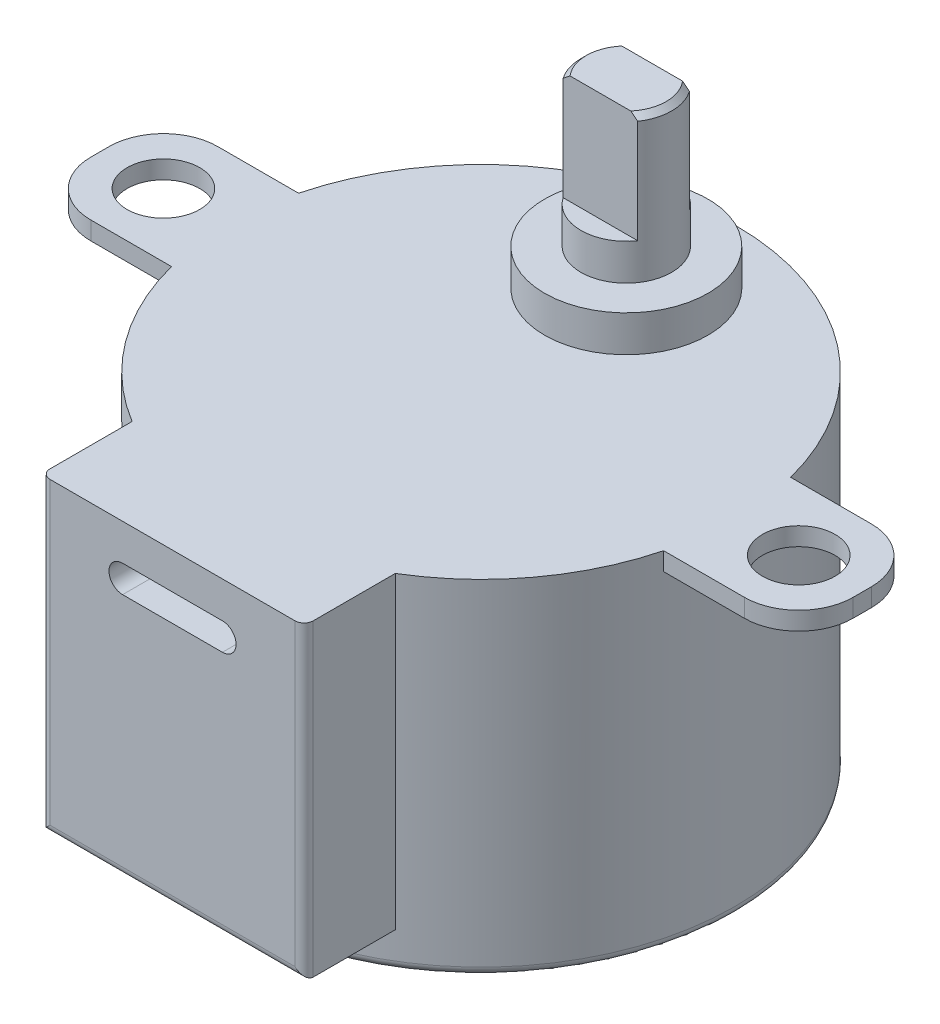
SolidWorks part; units mm, degrees
ref_plane "Спереди" through (0, 0, 0) normal (0, 0, 1) x (1, 0, 0)
ref_plane "Сверху" through (0, 0, 0) normal (0, 1, 0) x (1, 0, 0)
ref_plane "Справа" through (0, 0, 0) normal (1, 0, 0) x (0, 0, -1)
sketch "Эскиз1" plane through (0, 0, 0) normal (0, 1, 0) x (1, 0, 0)
  line L0 (-14, 0) -> (14, 0) construction
  line L1 (0, 14) -> (0, -14) construction
  circle A0 centre (0, 0) radius 14
extrude "Бобышка-Вытянуть1" add sketch "Эскиз1" along normal blind 19 contours A0
sketch "Эскиз2" plane through (0, 19, 0) normal (0, 1, 0) x (1, 0, 0)
  line L0 (-18, -3.5) -> (-13.5554, -3.5)
  line L1 (-18, 3.5) -> (-13.5554, 3.5)
  line L2 (-21, 0.5) -> (-21, -0.5)
  line L4 (0, -14) -> (0, 14) construction
  line L5 (-14, 0) -> (14, 0) construction
  line L7 (21, 0.5) -> (21, -0.5)
  line L8 (18, 3.5) -> (13.5554, 3.5)
  line L9 (18, -3.5) -> (13.5554, -3.5)
  arc A0 (-21, 0.5) -> (-18, 3.5) centre (-18, 0.5) cw
  arc A1 (-21, -0.5) -> (-18, -3.5) centre (-18, -0.5) ccw
  circle A2 centre (-17.5, 0) radius 2
  circle A3 centre (0, 0) radius 14 construction
  circle A4 centre (17.5, 0) radius 2
  arc A5 (21, -0.5) -> (18, -3.5) centre (18, -0.5) cw
  arc A6 (21, 0.5) -> (18, 3.5) centre (18, 0.5) ccw
  point P25 (21, 0)
  circle M6 centre (0, 0) radius 14
  dimension "D4" = 3.5
  dimension "D6" = 3
extrude "Бобышка-Вытянуть2" add sketch "Эскиз2" against normal blind 1 contours L7 A6 L8 L9 A5 A4 M6 | L2 A1 L0 L1 A0 A2 M6
sketch "Эскиз5" plane through (0, 19, 0) normal (0, 1, 0) x (1, 0, 0)
  line L1 (-7.25, -17) -> (7.25, -17)
  line L2 (7.25, -17) -> (7.25, -11.9765)
  line L3 (-7.25, -17) -> (-7.25, -11.9765)
  line L9 (-13.5554, 3.5) -> (-18, 3.5)
  line L10 (-21, 0.5) -> (-21, -0.5)
  line L11 (-18, -3.5) -> (-13.5554, -3.5)
  line L12 (13.5554, -3.5) -> (18, -3.5)
  line L13 (21, -0.5) -> (21, 0.5)
  line L14 (18, 3.5) -> (13.5554, 3.5)
  arc A0 (-13.5554, -3.5) -> (13.5554, -3.5) centre (0, 0) ccw construction
  arc A7 (13.5554, 3.5) -> (-13.5554, 3.5) centre (0, 0) ccw
  arc A8 (-18, 3.5) -> (-21, 0.5) centre (-18, 0.5) ccw
  arc A9 (-21, -0.5) -> (-18, -3.5) centre (-18, -0.5) ccw
  arc A10 (-13.5554, -3.5) -> (13.5554, -3.5) centre (0, 0) ccw
  arc A11 (18, -3.5) -> (21, -0.5) centre (18, -0.5) ccw
  arc A12 (21, 0.5) -> (18, 3.5) centre (18, 0.5) ccw
  arc A16 (-7.25, -11.9765) -> (7.25, -11.9765) centre (0, 0) ccw
  dimension "D1" = 0
extrude "Бобышка-Вытянуть3" add sketch "Эскиз5" against normal blind 17
sketch "Эскиз6" plane through (0, 19, 0) normal (0, 1, 0) x (1, 0, 0)
  circle A0 centre (0, 8) radius 4.5
  arc A2 (13.5554, 3.5) -> (-13.5554, 3.5) centre (0, 0) ccw construction
  point P5 (0, 14)
  point P6 (0, 12.5)
  dimension "D1" = 1.5
extrude "Бобышка-Вытянуть4" add sketch "Эскиз6" along normal blind 2
sketch "Эскиз7" plane through (0, 21, 0) normal (0, 1, 0) x (1, 0, 0)
  circle A0 centre (0, 8) radius 2.5
extrude "Бобышка-Вытянуть6" add sketch "Эскиз7" along normal blind 2
sketch "Эскиз9" plane through (0, 23, 0) normal (0, 1, 0) x (1, 0, 0)
  line L1 (-2.053, 9.4265) -> (2.053, 9.4265)
  line L3 (-2.053, 6.5735) -> (2.053, 6.5735)
  circle A0 centre (0, 8) radius 2.5 construction
  arc A1 (-2.053, 6.5735) -> (-2.053, 9.4265) centre (0, 8) cw
  arc A2 (2.053, 9.4265) -> (2.053, 6.5735) centre (0, 8) cw
  point P0 (0, 8)
extrude "Бобышка-Вытянуть8" add sketch "Эскиз9" along normal blind 6
sketch "Эскиз11" plane through (0, 0, 17) normal (0, 0, 1) x (1, 0, 0)
  line L0 (-2.75, 16.25) -> (2.75, 16.25) construction
  line L1 (-2.75, 17) -> (2.75, 17)
  line L2 (-2.75, 15.5) -> (2.75, 15.5)
  line L3 (-7.25, 19) -> (7.25, 19) construction
  line L4 (0, 19) -> (0, 13.0234) construction
  arc A0 (-2.75, 17) -> (-2.75, 15.5) centre (-2.75, 16.25) ccw
  arc A1 (2.75, 15.5) -> (2.75, 17) centre (2.75, 16.25) ccw
  point P2 (0, 16.25)
  point P9 (-3.5, 16.25)
  point P10 (3.5, 16.25)
  point P14 (-0.0513, 16.25)
  point P15 (-0.5159, 16.25)
  point P16 (0, 0)
  point P17 (0, 16.25)
  point P20 (0, 13.0234)
  dimension "D1" = 2
  dimension "D2" = 1.5
  dimension "D3" = 7
extrude "Вырез-Вытянуть1" cut sketch "Эскиз11" against normal blind 2
chamfer "Фаска4" distance 0.3 angle 45 2 edges at (2.5, 29, -8) (-2.5, 29, -8)
fillet "Скругление3" radius 0.5 3 edges at (7.25, 10.5, 17) (0, 2, 17) (-7.25, 10.5, 17)
fillet "Скругление4" radius 0.5 1 edges at (0, 0, 14)
